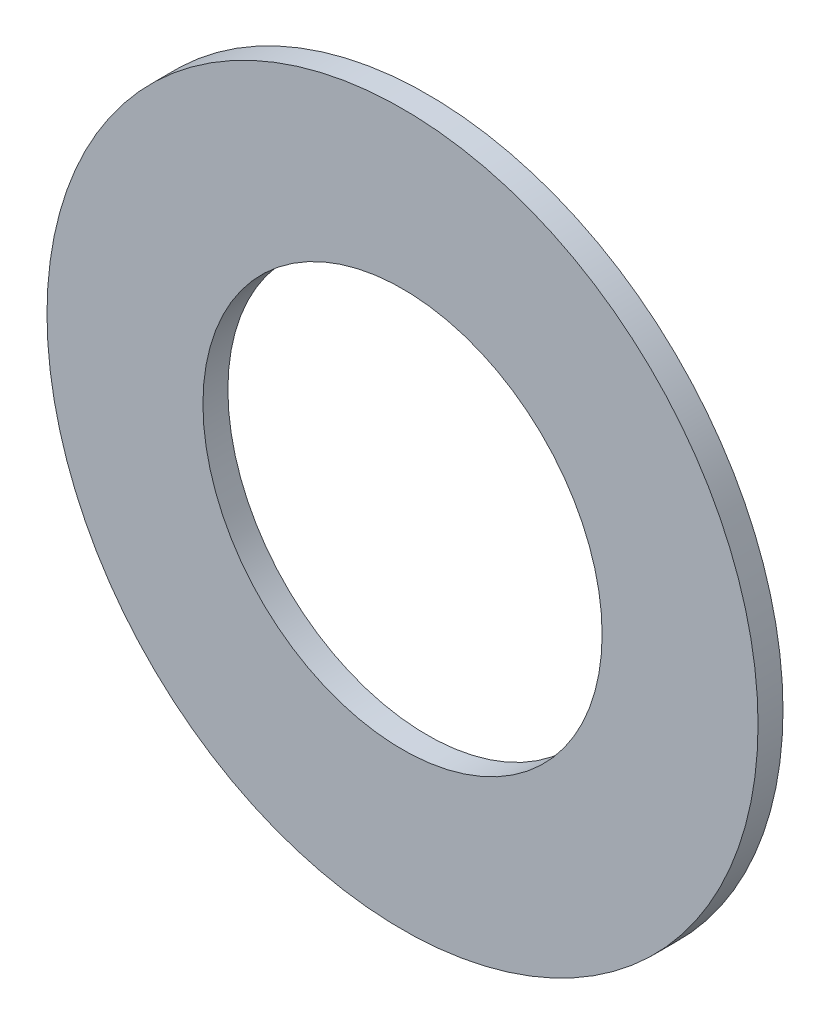
SolidWorks part; units mm, degrees
material "Nylon 101"
ref_plane "Front Plane" through (0, 0, 0) normal (0, 0, 1) x (1, 0, 0)
ref_plane "Top Plane" through (0, 0, 0) normal (0, 1, 0) x (1, 0, 0)
ref_plane "Right Plane" through (0, 0, 0) normal (1, 0, 0) x (0, 0, -1)
sketch "Sketch1" plane through (0, 0, 0) normal (0, 0, 1) x (1, 0, 0)
  circle A0 centre (0, 0) radius 4.064
  circle A1 centre (0, 0) radius 7.239
  dimension "ID" = 8.128
  dimension "OD" = 14.478
extrude "Extrude1" add sketch "Sketch1" against normal blind 0.508
